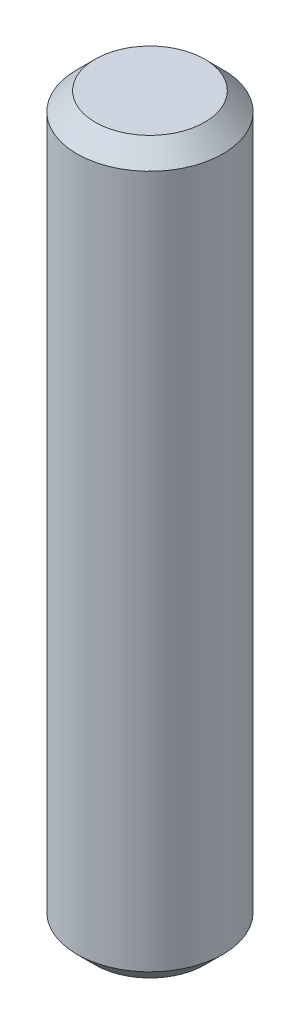
SolidWorks part; units mm, degrees
ref_plane "Front Plane" through (0, 0, 0) normal (0, 0, 1) x (1, 0, 0)
ref_plane "Top Plane" through (0, 0, 0) normal (0, 1, 0) x (1, 0, 0)
ref_plane "Right Plane" through (0, 0, 0) normal (1, 0, 0) x (0, 0, -1)
sketch "Sketch1" plane through (0, 0, 0) normal (0, 1, 0) x (1, 0, 0)
  circle A0 centre (0, 0) radius 0.2
  dimension "D1" = 0.4
extrude "Boss-Extrude1" add sketch "Sketch1" along normal blind 2
chamfer "Chamfer1" distance 0.05 angle 45 2 edges at (0, 0, 0.2) (0, 2, 0.2)
